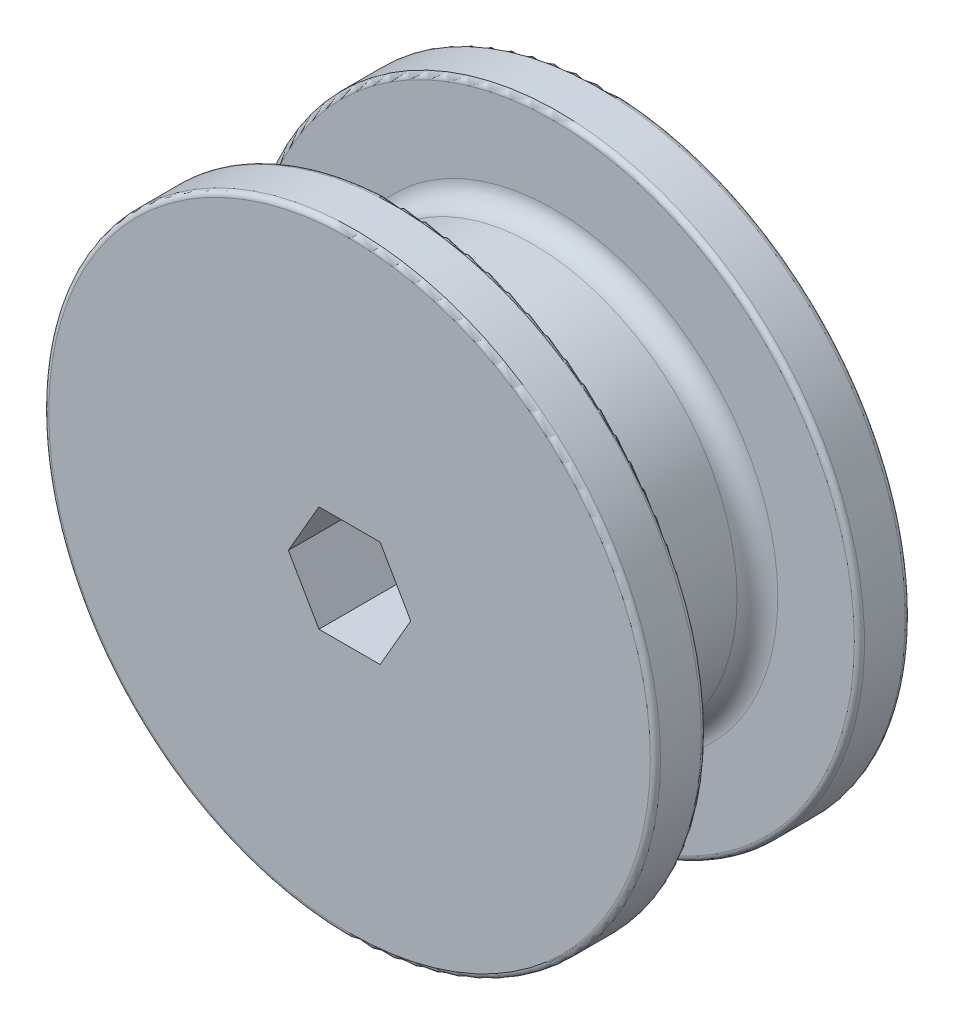
SolidWorks part; units mm, degrees
ref_plane "Front Plane" through (0, 0, 0) normal (0, 0, 1) x (1, 0, 0)
ref_plane "Top Plane" through (0, 0, 0) normal (0, 1, 0) x (1, 0, 0)
ref_plane "Right Plane" through (0, 0, 0) normal (1, 0, 0) x (0, 0, -1)
sketch "Sketch1" plane through (0, 0, 0) normal (0, 0, 1) x (1, 0, 0)
  circle A0 centre (0, 0) radius 25.4
  dimension "D1" = 50.8
extrude "Boss-Extrude1" add sketch "Sketch1" along normal blind 19.05
sketch "Sketch2" plane through (0, 0, 19.05) normal (0, 0, 1) x (1, 0, 0)
  circle A0 centre (0, 0) radius 38.1
  dimension "D1" = 76.2
extrude "Boss-Extrude2" add sketch "Sketch2" along normal blind 6.35
sketch "Sketch3" plane through (0, 0, 0) normal (0, 0, -1) x (-1, 0, 0)
  circle A0 centre (0, 0) radius 38.1
  dimension "D1" = 76.2
extrude "Boss-Extrude3" add sketch "Sketch3" along normal blind 6.35
sketch "Sketch4" plane through (0, 0, 25.4) normal (0, 0, 1) x (1, 0, 0)
  line L1 (7.621, 0) -> (3.8105, 6.6)
  line L2 (3.8105, 6.6) -> (-3.8105, 6.6)
  line L3 (-3.8105, 6.6) -> (-7.621, 0)
  line L4 (-7.621, 0) -> (-3.8105, -6.6)
  line L5 (-3.8105, -6.6) -> (3.8105, -6.6)
  line L6 (3.8105, -6.6) -> (7.621, 0)
  circle A0 centre (0, 0) radius 6.6 construction
  dimension "D1" = 13.2
extrude "Cut-Extrude1" cut sketch "Sketch4" against normal through all
fillet "Fillet1" radius 2.54 2 edges at (25.4, 0, 0) (25.4, 0, 19.05)
fillet "Fillet2" radius 0.635 4 edges at (38.1, 0, 19.05) (38.1, 0, 25.4) (-38.1, 0, 0) (-38.1, 0, -6.35)
